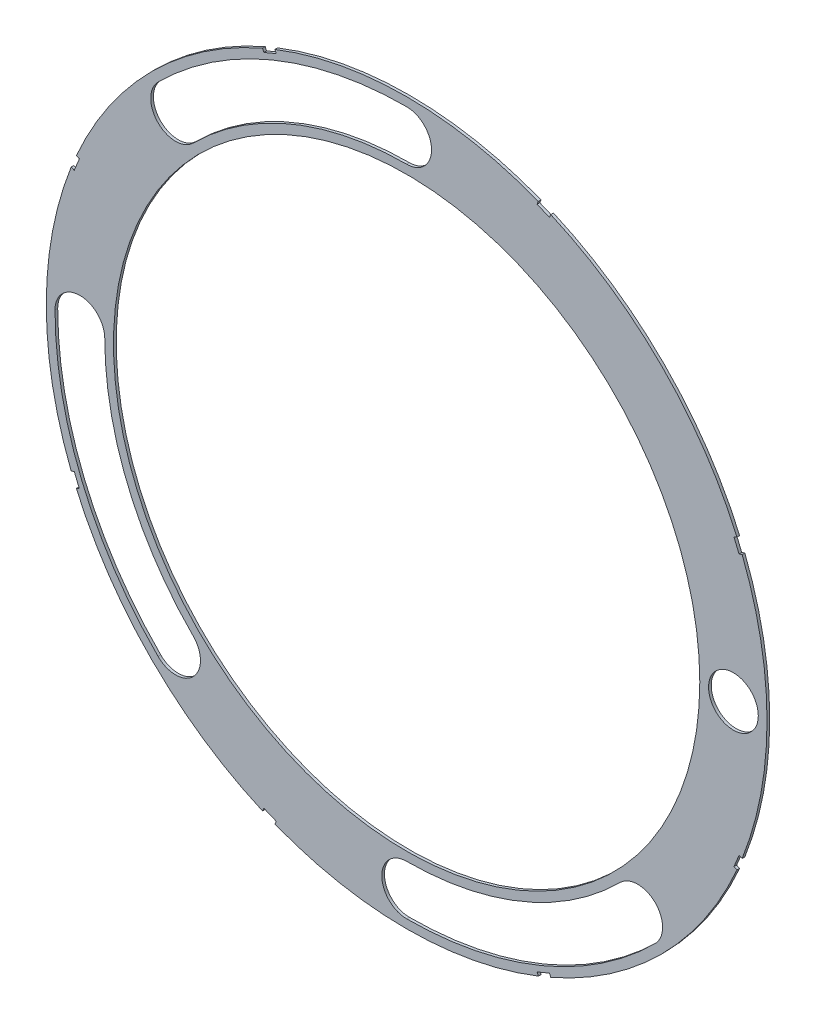
SolidWorks part; units mm, degrees
material "PTFE (general)"
ref_plane "Front Plane" through (0, 0, 0) normal (0, 0, 1) x (1, 0, 0)
ref_plane "Top Plane" through (0, 0, 0) normal (0, 1, 0) x (1, 0, 0)
ref_plane "Right Plane" through (0, 0, 0) normal (1, 0, 0) x (0, 0, -1)
sketch "Sketch4" plane through (0, 0, 0) normal (0, 0, 1) x (1, 0, 0)
  circle A0 centre (0, 0) radius 68.072
  dimension "D1" = 136.144
extrude "Boss-Extrude2" add sketch "Sketch4" along normal blind 0.508
sketch "Sketch5" plane through (0, 0, 0.508) normal (0, 0, 1) x (1, 0, 0)
  circle A0 centre (0, 0) radius 55.372
  circle A1 centre (0, 0) radius 68.072 construction
  dimension "D1" = 12.7
extrude "Cut-Extrude5" cut sketch "Sketch5" against normal through all
sketch "Sketch6" plane through (0, 0, 0.508) normal (0, 0, 1) x (1, 0, 0)
  line L0 (0, 0) -> (61.722, 0) construction
  line L1 (0, 0) -> (48.1342, -48.1342) construction
  line L2 (0, 0) -> (0, -68.072) construction
  line L3 (0, 0) -> (0, -68.072) construction
  line L4 (0, 0) -> (48.1342, -48.1342) construction
  line L5 (0, 0) -> (-48.1342, -48.1342) construction
  line L6 (0, 0) -> (-48.1342, -48.1342) construction
  line L7 (0, 0) -> (-68.072, 0) construction
  line L8 (0, 0) -> (-68.072, 0) construction
  line L9 (0, 0) -> (-48.1342, 48.1342) construction
  line L10 (0, 0) -> (-48.1342, 48.1342) construction
  line L11 (0, 0) -> (0, 68.072) construction
  line L12 (0, 0) -> (0, 68.072) construction
  line L13 (0, 0) -> (40.3213, -40.3214) construction
  line L14 (0, 0) -> (-40.3214, -40.3213) construction
  circle A0 centre (61.722, 0) radius 4.699
  circle A1 centre (0, 0) radius 68.072 construction
  arc A2 (46.9667, -46.9667) -> (40.3213, -40.3214) centre (43.644, -43.644) ccw
  arc A3 (40.3213, -40.3214) -> (0, -57.023) centre (0, 0) cw
  arc A4 (0, -57.023) -> (0, -66.421) centre (0, -61.722) ccw
  arc A5 (0, -66.421) -> (46.9667, -46.9667) centre (0, 0) ccw
  arc A6 (-46.9667, -46.9667) -> (-40.3214, -40.3213) centre (-43.644, -43.644) ccw
  arc A7 (-40.3214, -40.3213) -> (-57.023, 0) centre (0, 0) cw
  arc A8 (-66.421, 0) -> (-46.9667, -46.9667) centre (0, 0) ccw
  arc A9 (-57.023, 0) -> (-66.421, 0) centre (-61.722, 0) ccw
  arc A10 (-46.9667, 46.9667) -> (-40.3213, 40.3214) centre (-43.644, 43.644) ccw
  arc A11 (-40.3213, 40.3214) -> (0, 57.023) centre (0, 0) cw
  arc A12 (0, 66.421) -> (-46.9667, 46.9667) centre (0, 0) ccw
  arc A13 (0, 57.023) -> (0, 66.421) centre (0, 61.722) ccw
  circle A16 centre (0, 0) radius 55.372 construction
  point P4 (43.644, -43.644)
  point P11 (0, -61.722)
  point P13 (-43.644, -43.644)
  point P27 (-61.722, 0)
  point P30 (0, 0)
  point P36 (-43.644, 43.644)
  point P41 (0, 61.722)
  dimension "D2" = 9.398
  dimension "D3" = 45
  dimension "D4" = 90
  dimension "D1" = 6.35
  dimension "D6" = 6.35
  dimension "D7" = 9.398
  dimension "D8" = 4.699
  dimension "D9" = 4.699
  dimension "D5" = 6.35
  dimension "D10" = 90
extrude "Cut-Extrude6" cut sketch "Sketch6" against normal through all
sketch "Sketch8" plane through (0, 0, 0.508) normal (0, 0, 1) x (1, 0, 0)
  line L0 (63.963, 25.1197) -> (62.991, 27.4664)
  line L1 (63.963, 25.1197) -> (62.7897, 24.6337)
  line L2 (62.7897, 24.6337) -> (61.8177, 26.9803)
  line L3 (62.991, 27.4664) -> (61.8177, 26.9803)
  line L4 (63.963, 25.1197) -> (61.8177, 26.9803) construction
  line L5 (62.991, 27.4664) -> (62.7897, 24.6337) construction
  line L6 (0, 0) -> (68.072, 0) construction
  line L7 (-25.1197, 63.963) -> (-27.4664, 62.991)
  line L8 (-25.1197, 63.963) -> (-24.6337, 62.7897)
  line L9 (-27.4664, 62.991) -> (-26.9803, 61.8177)
  line L10 (-24.6337, 62.7897) -> (-26.9803, 61.8177)
  line L11 (-27.4664, 62.991) -> (-24.6337, 62.7897) construction
  line L12 (-25.1197, 63.963) -> (-26.9803, 61.8177) construction
  line L13 (-62.991, 27.4664) -> (-63.963, 25.1197)
  line L14 (-62.991, 27.4664) -> (-61.8177, 26.9803)
  line L15 (-61.8177, 26.9803) -> (-62.7897, 24.6337)
  line L16 (-63.963, 25.1197) -> (-62.7897, 24.6337)
  line L17 (-62.991, 27.4664) -> (-62.7897, 24.6337) construction
  line L18 (-63.963, 25.1197) -> (-61.8177, 26.9803) construction
  line L19 (-63.963, -25.1197) -> (-62.991, -27.4664)
  line L20 (-63.963, -25.1197) -> (-62.7897, -24.6337)
  line L21 (-62.7897, -24.6337) -> (-61.8177, -26.9803)
  line L22 (-62.991, -27.4664) -> (-61.8177, -26.9803)
  line L23 (-63.963, -25.1197) -> (-61.8177, -26.9803) construction
  line L24 (-62.991, -27.4664) -> (-62.7897, -24.6337) construction
  line L25 (-27.4664, -62.991) -> (-25.1197, -63.963)
  line L26 (-27.4664, -62.991) -> (-26.9803, -61.8177)
  line L27 (-26.9803, -61.8177) -> (-24.6337, -62.7897)
  line L28 (-25.1197, -63.963) -> (-24.6337, -62.7897)
  line L29 (-27.4664, -62.991) -> (-24.6337, -62.7897) construction
  line L30 (-25.1197, -63.963) -> (-26.9803, -61.8177) construction
  line L31 (25.1197, -63.963) -> (27.4664, -62.991)
  line L32 (25.1197, -63.963) -> (24.6337, -62.7897)
  line L33 (24.6337, -62.7897) -> (26.9803, -61.8177)
  line L34 (27.4664, -62.991) -> (26.9803, -61.8177)
  line L35 (25.1197, -63.963) -> (26.9803, -61.8177) construction
  line L36 (27.4664, -62.991) -> (24.6337, -62.7897) construction
  line L37 (62.991, -27.4664) -> (63.963, -25.1197)
  line L38 (62.991, -27.4664) -> (61.8177, -26.9803)
  line L39 (61.8177, -26.9803) -> (62.7897, -24.6337)
  line L40 (63.963, -25.1197) -> (62.7897, -24.6337)
  line L41 (62.991, -27.4664) -> (62.7897, -24.6337) construction
  line L42 (63.963, -25.1197) -> (61.8177, -26.9803) construction
  line L43 (27.4664, 62.991) -> (25.1197, 63.963)
  line L44 (27.4664, 62.991) -> (26.9803, 61.8177)
  line L45 (26.9803, 61.8177) -> (24.6337, 62.7897)
  line L46 (25.1197, 63.963) -> (24.6337, 62.7897)
  line L47 (27.4664, 62.991) -> (24.6337, 62.7897) construction
  line L48 (25.1197, 63.963) -> (26.9803, 61.8177) construction
  circle A0 centre (0, 0) radius 68.072 construction
  point P3 (-26.05, 62.8903)
  point P7 (62.8903, 26.05)
  point P11 (-62.8903, 26.05)
  point P20 (-62.8903, -26.05)
  point P25 (-26.05, -62.8903)
  point P26 (0, 0)
  point P31 (26.05, -62.8903)
  point P36 (62.8903, -26.05)
  point P43 (26.05, 62.8903)
  point P46 (0, 0)
  dimension "D5" = 1.27
  dimension "D6" = 2.54
  dimension "D7" = 1.27
  dimension "D9" = 0.635
  dimension "D10" = 112.5
  dimension "D14" = 0.635
  dimension "D21" = 22.5
  dimension "D24" = 0.635
  dimension "D11" = 8
extrude "Cut-Extrude11" cut sketch "Sketch8" against normal through all
